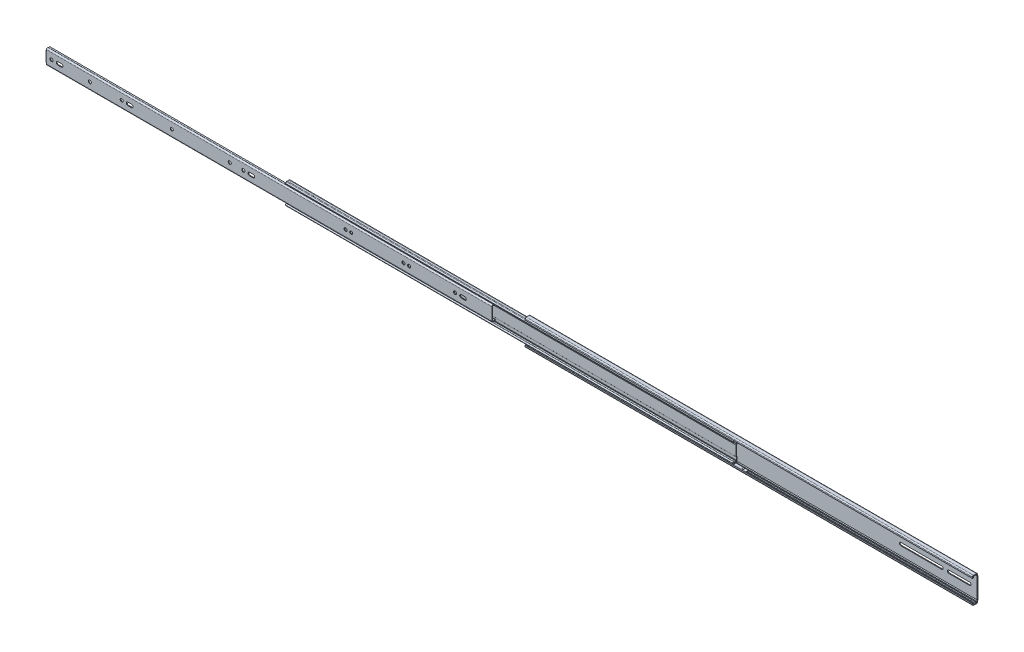
SolidWorks part; units mm, degrees
ref_plane "Front" through (0, 0, 0) normal (0, 0, 1) x (1, 0, 0)
ref_plane "Top" through (0, 0, 0) normal (0, 1, 0) x (1, 0, 0)
ref_plane "Right" through (0, 0, 0) normal (1, 0, 0) x (0, 0, -1)
sketch "Sketch1" plane through (0, 0, 0) normal (1, 0, 0) x (0, 0, -1)
  line L0 (-3.9878, 0) -> (4.7498, 0) construction
  line L1 (4.7498, 0) -> (3.556, 0)
  line L2 (3.556, 0) -> (3.556, 16.3322)
  line L3 (4.7498, 16.3322) -> (4.7498, 0)
  line L4 (2.794, 17.7546) -> (3.556, 16.3322)
  line L5 (3.9878, 17.7546) -> (4.7498, 16.3322)
  line L13 (-0.7049, 19.4437) -> (-2.286, 19.4437)
  line L111 (2.54, 19.4437) -> (0.7049, 19.4437)
  line L130 (2.794, 17.7546) -> (2.794, 19.1897)
  line L132 (3.9878, 19.1897) -> (3.9878, 17.7546)
  line L180 (-2.794, 17.0942) -> (-3.9878, 17.0942)
  line L190 (-2.794, 18.9357) -> (-2.794, 17.0942)
  line L191 (-3.9878, 17.0942) -> (-3.9878, 18.9357)
  line L194 (-2.286, 20.6375) -> (2.54, 20.6375)
  arc A0 (-2.286, 20.6375) -> (-3.9878, 18.9357) centre (-2.286, 18.9357) ccw
  arc A1 (3.9878, 19.1897) -> (2.54, 20.6375) centre (2.54, 19.1897) ccw
  arc A23 (2.794, 19.1897) -> (2.54, 19.4437) centre (2.54, 19.1897) ccw
  arc A26 (0.7049, 19.4437) -> (-0.7049, 19.4437) centre (0, 18.0213) ccw
  arc A44 (-2.286, 19.4437) -> (-2.794, 18.9357) centre (-2.286, 18.9357) ccw
  dimension "D7" = 1.7018
  dimension "D8" = 1.4478
  dimension "D9" = 1.5875
  dimension "D12" = 16.3322
  dimension "D13" = 1.4224
  dimension "D1" = 1.1938
  dimension "D2" = 1.1938
  dimension "D3" = 34.1884
  dimension "D4" = 41.275
  dimension "D5" = 8.7376
  dimension "D6" = 4.7498
  dimension "D10" = 36.0426
  dimension "D11" = 7.9756
extrude "Extrude1" add sketch "Sketch1" along normal blind 711.2
ref_plane "Plane1" through (-381, 0, 0) normal (1, 0, 0) x (0, 0, -1)
sketch "Sketch2" plane through (-381, 0, 0) normal (1, 0, 0) x (0, 0, -1)
  line L0 (-6.35, 0) -> (6.35, 0) construction
  line L1 (4.7498, 0) -> (4.7498, 16.3322) construction
  line L2 (2.0623, 7.6031) -> (2.0623, 0)
  line L35 (2.9464, 15.9258) -> (2.9464, 9.0869)
  line L55 (2.5223, 8.0632) -> (2.0623, 7.6031)
  line L116 (1.6782, 13.5661) -> (0.3308, 13.5661)
  line L183 (-4.0005, 15.0219) -> (-2.6824, 16.6835)
  arc A0 (0.3308, 13.5661) -> (-2.1317, 13.538) centre (-0.889, 12.5501) ccw
  arc A2 (-1.311, 17.0718) -> (-2.6824, 16.6835) centre (-1.7272, 15.9258) ccw
  arc A17 (2.5223, 8.0632) -> (2.9464, 9.0869) centre (1.4986, 9.0869) ccw
  arc A28 (2.9464, 15.9258) -> (1.311, 17.0718) centre (1.7272, 15.9258) ccw
  arc A37 (-1.311, 17.0718) -> (1.311, 17.0718) centre (0, 20.6815) ccw
  arc A46 (-4.0005, 15.0219) -> (-2.1317, 13.538) centre (-2.8002, 14.6147) ccw
  dimension "D5" = 1.4478
  dimension "D9" = 29.2294
  dimension "D10" = 31.8516
  dimension "D11" = 1.2192
  dimension "D13" = 41.3631
  dimension "D15" = 1.5875
  dimension "D18" = 1.2674
  dimension "D2" = 2.6875
  dimension "D3" = 5.7466
  dimension "D4" = 0.8841
  dimension "D6" = 135
  dimension "D7" = 7.6031
  dimension "D8" = 27.1322
  dimension "D14" = 38.424
  dimension "D16" = 25.1002
  dimension "D17" = 2.9513
  dimension "D19" = 3.4544
  dimension "D20" = 1.6616
  dimension "D21" = 1.2682
extrude "Extrude-Thin3" add sketch "Sketch2" along normal blind 711.2 thin
ref_plane "Plane2" through (-762, 0, 0) normal (1, 0, 0) x (0, 0, -1)
sketch "Sketch3" plane through (-762, 0, 0) normal (1, 0, 0) x (0, 0, -1)
  line L0 (-6.35, 0) -> (6.35, 0) construction
  line L1 (4.7498, 0) -> (4.7498, 16.3322) construction
  line L146 (-4.7752, 0) -> (-4.7752, 9.9793)
  arc A5 (-1.9175, 11.4913) -> (0.3002, 11.6135) centre (-0.8886, 13.0032) ccw
  arc A41 (-1.9175, 11.4913) -> (-4.7752, 9.9793) centre (-2.9464, 9.9793) ccw
  dimension "D2" = 19.9587
  dimension "D3" = 26.0063
  dimension "D5" = 1.8288
  dimension "D1" = 9.525
  dimension "D4" = 5.0754
extrude "Extrude-Thin4" add sketch "Sketch3" along normal blind 709.93 thin
sketch "Sketch4" plane through (0, 0, 4.7752) normal (0, 0, 1) x (1, 0, 0)
  line L0 (-762, 0) -> (-762, 9.9793) construction
  line L1 (-762, 11.8081) -> (-760.2982, 11.8081)
  line L2 (-762, 11.8081) -> (-762, 8.001)
  line L3 (-762, 8.001) -> (-760.2982, 8.001)
  line L4 (-760.2982, 11.8081) -> (-760.2982, 8.001)
  line L5 (-52.07, 11.8081) -> (-762, 11.8081) construction
  line L6 (-764.2506, 0) -> (-759.0921, 0) construction
  line L7 (-52.07, 0) -> (-762, 0) construction
  dimension "D1" = 1.7018
  dimension "D2" = 16.002
extrude "Cut-Extrude1" cut sketch "Sketch4" against normal through all
sketch "Sketch5" plane through (0, 0, 4.7752) normal (0, 0, 1) x (1, 0, 0)
  line L0 (-52.07, 0) -> (-762, 0) construction
  line L1 (-762, 8.001) -> (-760.8062, 8.001)
  line L2 (-762, 8.001) -> (-762, 0)
  line L3 (-762, 0) -> (-760.8062, 0)
  line L4 (-760.8062, 8.001) -> (-760.8062, 0)
  dimension "D1" = 1.1938
extrude "Extrude2" add sketch "Sketch5" against normal blind 6.9088
fillet "Fillet1" radius 0.508 1 edges at (-760.8062, 4.0005, 3.5814)
fillet "Fillet2" radius 1.7018 2 edges at (-761.1491, 8.001, 4.7752) (-762, 4.0005, 4.7752)
sketch "Sketch6" plane through (0, 0, 4.7752) normal (0, 0, 1) x (1, 0, 0)
  line L0 (-52.07, 0) -> (-760.2982, 0) construction
  line L1 (-762, 0) -> (-762, 8.001) construction
  line L2 (-739.394, 2.4384) -> (-739.394, -2.4384) construction
  line L3 (-736.5873, -2.4384) -> (-742.2007, -2.4384)
  line L4 (-742.2007, 2.4384) -> (-736.5873, 2.4384)
  line L5 (-627.888, 2.4384) -> (-627.888, -2.4384) construction
  line L6 (-625.0813, -2.4384) -> (-630.6947, -2.4384)
  line L7 (-630.6947, 2.4384) -> (-625.0813, 2.4384)
  circle A0 centre (-752.094, 0) radius 2.4384
  arc A1 (-742.2007, -2.4384) -> (-742.2007, 2.4384) centre (-742.2007, 0) cw
  arc A2 (-736.5873, 2.4384) -> (-736.5873, -2.4384) centre (-736.5873, 0) cw
  circle A3 centre (-691.388, 0) radius 2.4384
  circle A4 centre (-640.588, 0) radius 2.4384
  arc A5 (-630.6947, -2.4384) -> (-630.6947, 2.4384) centre (-630.6947, 0) cw
  arc A6 (-625.0813, 2.4384) -> (-625.0813, -2.4384) centre (-625.0813, 0) cw
  dimension "D1" = 9.906
  dimension "D2" = 4.8768
  dimension "D3" = 10.4902
  dimension "D5" = 60.706
  dimension "D6" = 111.506
  dimension "D4" = 12.7
  dimension "D7" = 12.7
extrude "Cut-Extrude2" cut sketch "Sketch6" against normal up to next (1.1938 mm away)
sketch "Sketch7" plane through (0, 0, 4.7752) normal (0, 0, 1) x (1, 0, 0)
  line L0 (-52.07, 0) -> (-622.6429, 0) construction
  circle A0 centre (-560.959, 0) radius 2.4384
  arc A1 (-749.6556, 0) -> (-754.5324, 0) centre (-752.094, 0) ccw construction
  dimension "Cut A" = 191.135
extrude "Cut A" cut sketch "Sketch7" against normal up to next (1.1938 mm away)
sketch "Sketch8" plane through (33.2857, 2.8338, 4.7752) normal (0, 0, 1) x (1, 0, 0)
  line L1 (-85.3557, -2.8338) -> (-591.8063, -2.8338) construction
  circle A0 centre (-502.1697, -2.8338) radius 2.4384
  arc A2 (-782.9413, -2.8338) -> (-787.8181, -2.8338) centre (-785.3797, -2.8338) ccw construction
  dimension "Cut B" = 283.21
extrude "Cut B" cut sketch "Sketch8" against normal up to next (1.1938 mm away)
sketch "Sketch9" plane through (0, 0, 4.7752) normal (0, 0, 1) x (1, 0, 0)
  line L0 (-52.07, 0) -> (-466.4456, 0) construction
  line L1 (-736.5873, 2.4384) -> (-742.2007, 2.4384) construction
  line L3 (-434.594, 2.4384) -> (-434.594, -2.4384) construction
  line L4 (-431.7873, -2.4384) -> (-437.4007, -2.4384)
  line L5 (-437.4007, 2.4384) -> (-431.7873, 2.4384)
  arc A0 (-749.6556, 0) -> (-754.5324, 0) centre (-752.094, 0) ccw construction
  circle A4 centre (-447.294, 0) radius 2.4384
  arc A5 (-437.4007, -2.4384) -> (-437.4007, 2.4384) centre (-437.4007, 0) cw
  arc A6 (-431.7873, 2.4384) -> (-431.7873, -2.4384) centre (-431.7873, 0) cw
  dimension "D1" = 12.7
  dimension "Cut C" = 304.8
extrude "Cut C" cut sketch "Sketch9" against normal up to next (1.1938 mm away)
sketch "Sketch10" plane through (0, 0, 4.7752) normal (0, 0, 1) x (1, 0, 0)
  line L0 (-52.07, 0) -> (-429.3489, 0) construction
  circle A0 centre (-284.734, 0) radius 2.4384
  circle A1 centre (-275.844, 0) radius 2.4384
  arc A2 (-749.6556, 0) -> (-754.5324, 0) centre (-752.094, 0) ccw construction
  dimension "D1" = 8.89
  dimension "Cut D" = 467.36
extrude "Cut D" cut sketch "Sketch10" against normal up to next (1.1938 mm away)
sketch "Sketch11" plane through (55.8477, 2.1411, 4.7752) normal (0, 0, 1) x (1, 0, 0)
  line L1 (-107.9177, -2.1411) -> (-329.2533, -2.1411) construction
  circle A0 centre (-248.5067, -2.1411) radius 2.4384
  circle A1 centre (-239.6167, -2.1411) radius 2.4384
  arc A3 (-805.5033, -2.1411) -> (-810.3801, -2.1411) centre (-807.9417, -2.1411) ccw construction
  dimension "D1" = 8.89
  dimension "Cut E" = 559.435
extrude "Cut E" cut sketch "Sketch11" against normal up to next (1.1938 mm away)
sketch "Sketch12" plane through (338.8914, 2.4625, 4.7752) normal (0, 0, 1) x (1, 0, 0)
  line L2 (-390.9614, -2.4625) -> (-520.222, -2.4625) construction
  line L3 (-436.9354, -0.0241) -> (-436.9354, -2.4384) construction
  line L4 (-439.7421, -4.9009) -> (-434.1287, -4.9009)
  line L5 (-434.1287, -0.0241) -> (-439.7421, -0.0241)
  line L6 (-1075.4787, -0.0241) -> (-1081.0921, -0.0241) construction
  arc A1 (-1088.547, -2.4625) -> (-1093.4238, -2.4625) centre (-1090.9854, -2.4625) ccw construction
  arc A2 (-439.7421, -0.0241) -> (-439.7421, -4.9009) centre (-439.7421, -2.4625) ccw
  arc A3 (-434.1287, -0.0241) -> (-434.1287, -4.9009) centre (-434.1287, -2.4625) cw
  circle A4 centre (-449.6354, -2.4625) radius 2.4384
  dimension "D1" = 12.7
  dimension "Cut F" = 641.35
extrude "Cut F" cut sketch "Sketch12" against normal up to next (1.1938 mm away)
sketch "Sketch13" plane through (0, 0, -3.556) normal (0, 0, 1) x (1, 0, 0)
  line L0 (711.2, 0) -> (0, 0) construction
  line L1 (0, 16.3322) -> (0, 0) construction
  line L2 (43.942, 2.286) -> (57.658, 2.286)
  line L3 (57.658, -2.286) -> (43.942, -2.286)
  line L4 (665.988, 2.286) -> (699.262, 2.286)
  line L5 (699.262, -2.286) -> (665.988, -2.286)
  line L6 (589.788, 2.286) -> (654.812, 2.286)
  line L7 (654.812, -2.286) -> (589.788, -2.286)
  line L8 (711.2, 16.3322) -> (711.2, 0) construction
  circle A0 centre (12.7, 0) radius 2.286
  circle A1 centre (25.4, 0) radius 2.286
  arc A2 (43.942, 2.286) -> (43.942, -2.286) centre (43.942, 0) ccw
  arc A3 (57.658, -2.286) -> (57.658, 2.286) centre (57.658, 0) ccw
  arc A4 (665.988, 2.286) -> (665.988, -2.286) centre (665.988, 0) ccw
  arc A5 (699.262, -2.286) -> (699.262, 2.286) centre (699.262, 0) ccw
  arc A6 (589.788, 2.286) -> (589.788, -2.286) centre (589.788, 0) ccw
  arc A7 (654.812, -2.286) -> (654.812, 2.286) centre (654.812, 0) ccw
  dimension "D1" = 4.572
  dimension "D2" = 12.7
  dimension "D3" = 12.7
  dimension "D4" = 18.288
  dimension "D5" = 28.956
  dimension "D6" = 69.596
  dimension "D7" = 37.846
  dimension "D8" = 9.652
  dimension "D9" = 76.2
extrude "Cut-Extrude9" cut sketch "Sketch13" against normal up to next (1.1938 mm away)
mirror "Mirror1" about plane through (0, 0, 0) normal (0, 1, 0) of bodies 109 119 120
ref_plane "Plane3" through (12.7, 0, 0) normal (1, 0, 0) x (0, 0, -1)
sketch "Sketch14" plane through (12.7, 0, 0) normal (1, 0, 0) x (0, 0, -1)
  line L0 (0, 19.6088) -> (0, 16.8411)
  line L1 (0, 20.062) -> (0, 16.4217) construction
  arc A0 (0, 16.8411) -> (0, 19.6088) centre (0, 18.2249) ccw
  arc A4 (-1.311, 17.0718) -> (1.311, 17.0718) centre (0, 20.6815) ccw construction
  arc A5 (0.7049, 19.4437) -> (-0.7049, 19.4437) centre (0, 18.0213) ccw construction
  point P2 (0, 18.0213)
revolve "Revolve1" add sketch "Sketch14" angle 360 about L1
pattern_linear "LPattern1" count 14 spacing 25.4 along (1, 0, 0) of bodies 124
sketch "Sketch15" plane through (12.7, 0, 0) normal (1, 0, 0) x (0, 0, -1)
  line L0 (2.794, 19.1897) -> (2.794, 17.7546) construction
  line L1 (-2.032, 18.6059) -> (2.032, 18.6059)
  line L2 (-2.032, 18.6059) -> (-2.032, 17.8439)
  line L3 (-2.032, 17.8439) -> (2.032, 17.8439)
  line L4 (2.032, 18.6059) -> (2.032, 17.8439)
  line L5 (-2.794, 17.0942) -> (-2.794, 18.9357) construction
  line L6 (-1.3839, 18.2249) -> (1.3839, 18.2249) construction
  circle A0 centre (0, 18.2249) radius 1.3839 construction
  point P12 (0, 18.2249)
  dimension "D1" = 0.762
  dimension "D2" = 0.762
  dimension "D3" = 0.762
extrude "Extrude3" add sketch "Sketch15" along normal blind 336.55 and the other way blind 6.35
ref_plane "Plane4" through (-368.3, 0, 0) normal (1, 0, 0) x (0, 0, -1)
sketch "Sketch16" plane through (-368.3, 0, 0) normal (1, 0, 0) x (0, 0, -1)
  line L0 (-0.889, 14.1376) -> (-0.889, 11.1744)
  line L1 (-0.889, 14.5765) -> (-0.889, 10.6948) construction
  arc A0 (-0.889, 11.1744) -> (-0.889, 14.1376) centre (-0.889, 12.656) ccw
  arc A2 (-1.9175, 11.4913) -> (0.3002, 11.6135) centre (-0.8886, 13.0032) ccw construction
  arc A3 (0.3308, 13.5661) -> (-2.1317, 13.538) centre (-0.889, 12.5501) ccw construction
  point P8 (-0.889, 12.5501)
revolve "Revolve2" add sketch "Sketch16" angle 360 about L1
pattern_linear "LPattern2" count 12 spacing 25.4 along (1, 0, 0) of bodies 139
sketch "Sketch17" plane through (-368.3, 0, 0) normal (1, 0, 0) x (0, 0, -1)
  line L0 (-2.3706, 12.656) -> (0.5926, 12.656) construction
  line L1 (-2.8194, 13.037) -> (0.9906, 13.037)
  line L2 (-2.8194, 13.037) -> (-2.8194, 12.275)
  line L3 (-2.8194, 12.275) -> (0.9906, 12.275)
  line L4 (0.9906, 13.037) -> (0.9906, 12.275)
  line L5 (1.7526, 15.9258) -> (1.7526, 9.0869) construction
  line L7 (-3.5814, -9.9793) -> (-3.5814, 9.9793) construction
  circle A0 centre (-0.889, 12.656) radius 1.4816 construction
  point P8 (-0.889, 12.656)
  dimension "D1" = 0.762
  dimension "D2" = 0.762
  dimension "D3" = 0.762
extrude "Extrude4" add sketch "Sketch17" along normal blind 285.75 and the other way blind 6.35
mirror "Mirror2" about plane through (0, 0, 0) normal (0, 1, 0) of bodies 138 151
equation "\"D1@Extrude-Thin4\"=\"Length@Extrude1\"-.05"
equation "\"D1@LPattern1\"=int(\"Length@Extrude1\"/2)"
equation "\"D1@Extrude3\" = (\"Length@Extrude1\"/2)-.75"
equation "\"D1@Extrude4\" = (\"Length@Extrude1\"/2)-2.75"
equation "\"Length@Extrude-Thin3\"=\"Length@Extrude1\""
